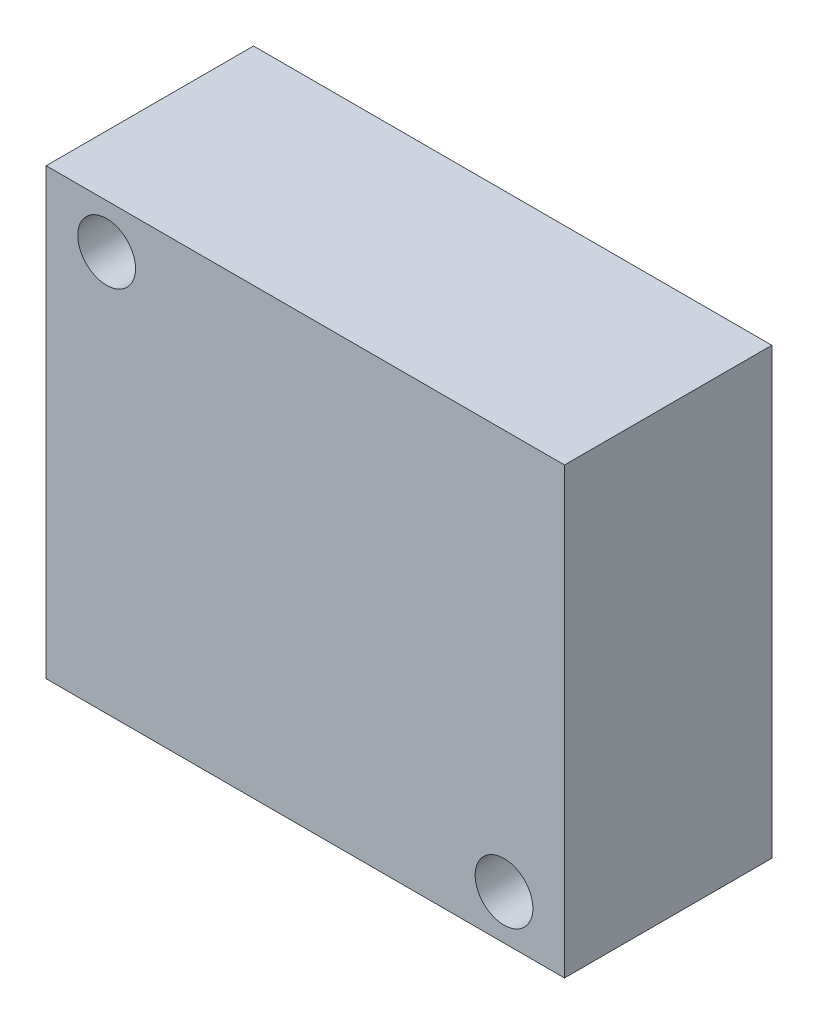
SolidWorks part; units mm, degrees
ref_plane "Plan de face" through (0, 0, 0) normal (0, 0, 1) x (1, 0, 0)
ref_plane "Plan de dessus" through (0, 0, 0) normal (0, 1, 0) x (1, 0, 0)
ref_plane "Plan de droite" through (0, 0, 0) normal (1, 0, 0) x (0, 0, -1)
sketch "Esquisse1" plane through (0, 0, 0) normal (0, 0, 1) x (1, 0, 0)
  line L1 (-17.5, -15) -> (17.5, -15)
  line L2 (-17.5, -15) -> (-17.5, 15)
  line L3 (-17.5, 15) -> (17.5, 15)
  line L4 (17.5, -15) -> (17.5, 15)
  line L5 (-17.5, -15) -> (17.5, 15) construction
  line L6 (-17.5, 15) -> (17.5, -15) construction
  point P0 (0, 0)
  dimension "D1" = 35
  dimension "D2" = 30
extrude "Boss.-Extru.1" add sketch "Esquisse1" along normal blind 14
sketch "Esquisse2" plane through (0, 0, 14) normal (0, 0, 1) x (1, 0, 0)
  line L1 (-13.4164, -12) -> (13.4164, -12)
  line L2 (-13.4164, -12) -> (-13.4164, 12)
  line L3 (-13.4164, 12) -> (13.4164, 12)
  line L4 (13.4164, -12) -> (13.4164, 12)
  line L5 (-13.4164, -12) -> (13.4164, 12) construction
  line L6 (-13.4164, 12) -> (13.4164, -12) construction
  point P0 (0, 0)
  dimension "D1" = 36
  dimension "D2" = 24
hole_wizard "Dégagement M3.51" positions "Esquisse4" profile "Esquisse5" hole size "M3.5" standard "Iso" end condition through all
sketch "Esquisse4" plane through (0, 0, 14) normal (0, 0, 1) x (1, 0, 0)
  point P0 (-13.4164, 12)
  point P3 (13.4164, -12)
sketch "Esquisse5" plane through (-13.4164, 12, 14) normal (1, 0, 0) x (0, -1, 0)
  line L0 (0, 0) -> (0, 14)
  line L1 (0, 14) -> (1.95, 14)
  line L2 (1.95, 14) -> (1.95, 0)
  line L5 (1.95, 0) -> (0, 0)
  line L11 (0, -6.35) -> (0, 107.95) construction
  dimension "Diamètre du perçage jusqu'au prochain" = 3.9
  dimension "Profondeur du perçage jusqu'au prochain" = 14
